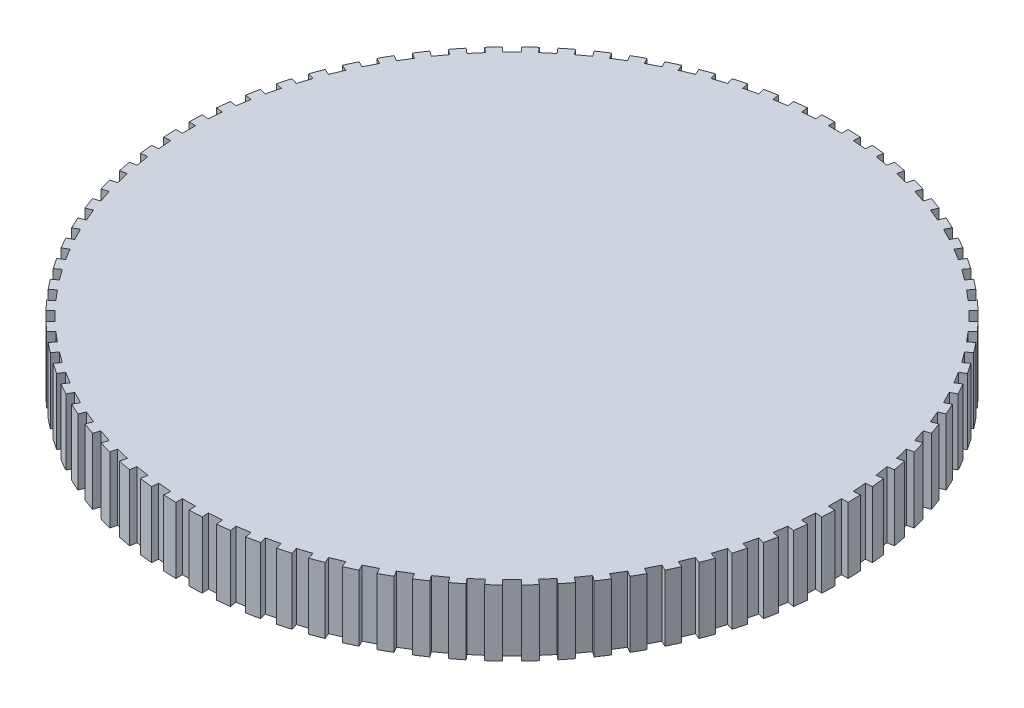
SolidWorks part; units mm, degrees
ref_plane "前视" through (0, 0, 0) normal (0, 0, 1) x (1, 0, 0)
ref_plane "上视" through (0, 0, 0) normal (0, 1, 0) x (1, 0, 0)
ref_plane "右视" through (0, 0, 0) normal (1, 0, 0) x (0, 0, -1)
sketch "草图1" plane through (0, 0, 0) normal (0, 1, 0) x (1, 0, 0)
  circle A0 centre (0, 0) radius 12.5
  dimension "D1" = 25
extrude "凸台-拉伸1" add sketch "草图1" along normal blind 2.5
sketch "草图2" plane through (0, 2.5, 0) normal (0, 1, 0) x (1, 0, 0)
  line L1 (12.25, 0.25) -> (12.75, 0.25)
  line L2 (12.25, 0.25) -> (12.25, -0.25)
  line L3 (12.25, -0.25) -> (12.75, -0.25)
  line L4 (12.75, 0.25) -> (12.75, -0.25)
  line L5 (12.25, 0.25) -> (12.75, -0.25) construction
  line L6 (12.25, -0.25) -> (12.75, 0.25) construction
  circle A0 centre (0, 0) radius 12.5 construction
  point P0 (12.5, 0)
  dimension "D1" = 0.5
  dimension "D2" = 0.5
extrude "切除-拉伸1" cut sketch "草图2" against normal blind 5.5
pattern_circular "阵列(圆周)1" count 80 over 360 about axis through (0, 0, 0) along (0, 1, 0) of "切除-拉伸1"
